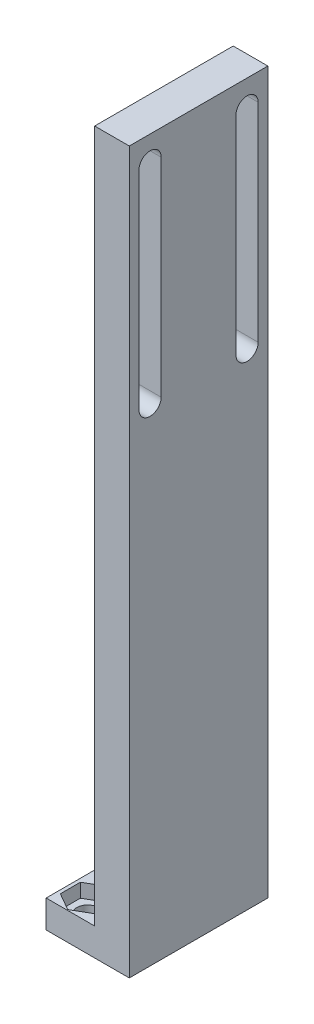
SolidWorks part; units mm, degrees
ref_plane "Front Plane" through (0, 0, 0) normal (0, 0, 1) x (1, 0, 0)
ref_plane "Top Plane" through (0, 0, 0) normal (0, 1, 0) x (1, 0, 0)
ref_plane "Right Plane" through (0, 0, 0) normal (1, 0, 0) x (0, 0, -1)
sketch "Sketch1" plane through (0, 0, 0) normal (0, 1, 0) x (1, 0, 0)
  line L1 (-6, 10) -> (6, 10)
  line L2 (-6, 10) -> (-6, -10)
  line L3 (-6, -10) -> (6, -10)
  line L4 (6, 10) -> (6, -10)
  line L5 (-6, 10) -> (6, -10) construction
  line L6 (-6, -10) -> (6, 10) construction
  circle A0 centre (-3, 7) radius 1.6
  circle A1 centre (-3, -7) radius 1.6
  point P0 (0, 0)
  dimension "D1" = 20
  dimension "D2" = 12
  dimension "D3" = 3
  dimension "D4" = 3
  dimension "D5" = 3
  dimension "D6" = 3
extrude "Boss-Extrude1" add sketch "Sketch1" along normal blind 4
sketch "Sketch18" plane through (0, 4, 0) normal (0, 1, 0) x (1, 0, 0)
  line L0 (6, 10) -> (-6, 10) construction
  line L1 (1, 10) -> (6, 10)
  line L2 (1, 10) -> (1, -10)
  line L3 (1, -10) -> (6, -10)
  line L4 (6, 10) -> (6, -10)
  dimension "D1" = 5
extrude "Boss-Extrude3" add sketch "Sketch18" along normal blind 100
sketch "Sketch20" plane through (0, 4, 0) normal (0, 1, 0) x (1, 0, 0)
  line L1 (-0.4944, 5.5238) -> (-0.4687, 8.4318)
  line L2 (-0.4687, 8.4318) -> (-2.9744, 9.9081)
  line L3 (-2.9744, 9.9081) -> (-5.5056, 8.4762)
  line L4 (-5.5056, 8.4762) -> (-5.5313, 5.5682)
  line L5 (-5.5313, 5.5682) -> (-3.0256, 4.0919)
  line L6 (-3.0256, 4.0919) -> (-0.4944, 5.5238)
  line L7 (-0.4944, -8.4415) -> (-0.4988, -5.5508)
  line L8 (-0.4988, -5.5508) -> (-3.0045, -4.1093)
  line L9 (-3.0045, -4.1093) -> (-5.5056, -5.5585)
  line L10 (-5.5056, -5.5585) -> (-5.5012, -8.4492)
  line L11 (-5.5012, -8.4492) -> (-2.9955, -9.8907)
  line L12 (-2.9955, -9.8907) -> (-0.4944, -8.4415)
  circle A0 centre (-3, 7) radius 2.5185 construction
  circle A1 centre (-3, -7) radius 2.5034 construction
extrude "Cut-Extrude4" cut sketch "Sketch20" against normal blind 2
sketch "Sketch21" plane through (6, 0, 0) normal (1, 0, 0) x (0, 0, -1)
  line L0 (-7, 100.3049) -> (-7, 70.3049) construction
  line L1 (-5.4, 100.3049) -> (-5.4, 70.3049)
  line L2 (-8.6, 100.3049) -> (-8.6, 70.3049)
  line L3 (7, 100.1703) -> (7, 70.1703) construction
  line L4 (8.6, 100.1703) -> (8.6, 70.1703)
  line L5 (5.4, 100.1703) -> (5.4, 70.1703)
  line L6 (-10, 104) -> (-10, 0) construction
  arc A0 (-5.4, 100.3049) -> (-8.6, 100.3049) centre (-7, 100.3049) ccw
  arc A1 (-8.6, 70.3049) -> (-5.4, 70.3049) centre (-7, 70.3049) ccw
  arc A2 (8.6, 100.1703) -> (5.4, 100.1703) centre (7, 100.1703) ccw
  arc A3 (5.4, 70.1703) -> (8.6, 70.1703) centre (7, 70.1703) ccw
  point P2 (-7, 85.3049)
  point P7 (0, 0)
  point P10 (7, 85.1703)
  point P15 (0, 0)
  dimension "D1" = 14
  dimension "D2" = 3
extrude "Cut-Extrude5" cut sketch "Sketch21" against normal blind 5
